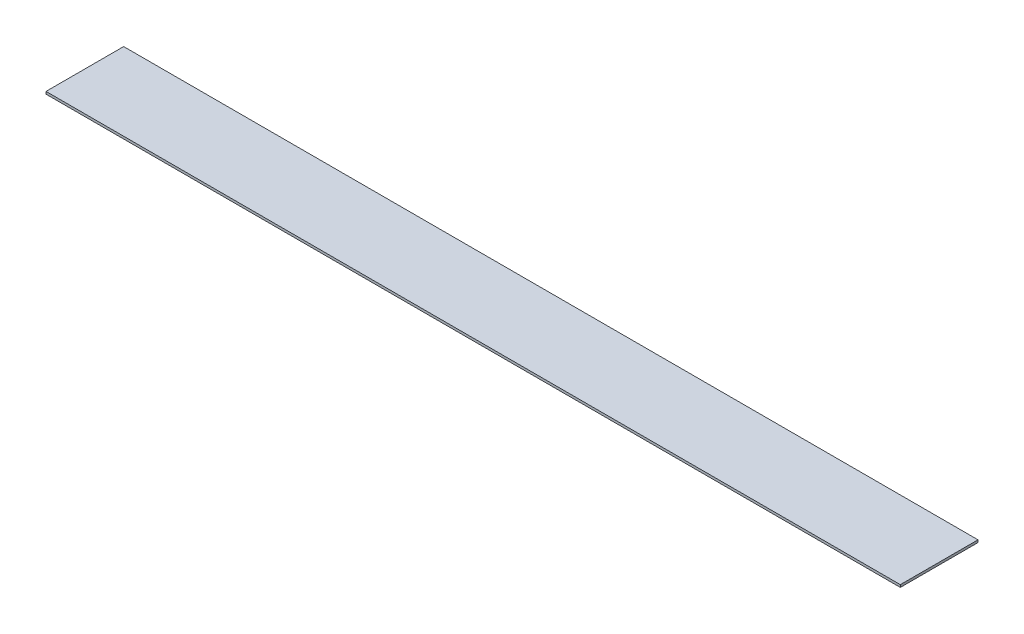
SolidWorks part; units mm, degrees
material "Nylon 101"
ref_plane "Front Plane" through (0, 0, 0) normal (0, 0, 1) x (1, 0, 0)
ref_plane "Top Plane" through (0, 0, 0) normal (0, 1, 0) x (1, 0, 0)
ref_plane "Right Plane" through (0, 0, 0) normal (1, 0, 0) x (0, 0, -1)
sketch "Sketch1" plane through (0, -80.2624, 0) normal (0, -1, 0) x (1, 0, 0)
  line L2 (0, 0) -> (558.8, 0)
  line L3 (0, 0) -> (0, 50.8)
  line L4 (0, 50.8) -> (558.8, 50.8)
  line L5 (558.8, 0) -> (558.8, 50.8)
  dimension "D2" = 558.8
  dimension "D1" = 50.8
extrude "Boss-Extrude1" add sketch "Sketch1" along normal blind 1.5875
